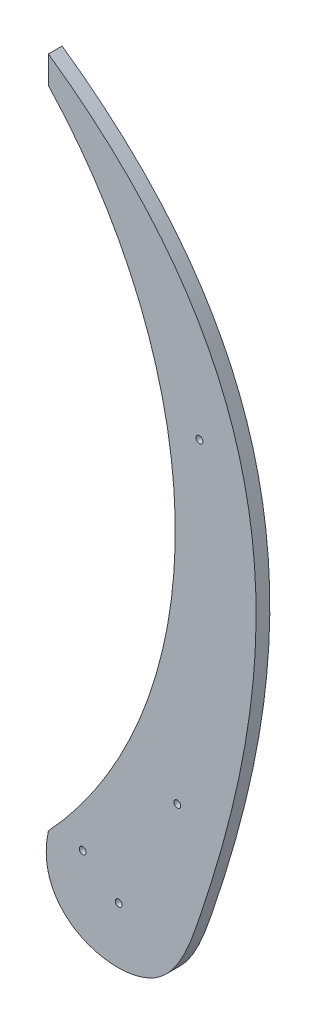
SolidWorks part; units mm, degrees
material "Mahogany"
ref_plane "Front Plane" through (0, 0, 0) normal (0, 0, 1) x (1, 0, 0)
ref_plane "Top Plane" through (0, 0, 0) normal (0, 1, 0) x (1, 0, 0)
ref_plane "Right Plane" through (0, 0, 0) normal (1, 0, 0) x (0, 0, -1)
sketch "Sketch2" plane through (0, 0, 0) normal (0, 0, 1) x (1, 0, 0)
  line L0 (0, 0) -> (110, 0) construction
  line L1 (55, 0) -> (55, -60) construction
  line L2 (0, 490) -> (0, 470)
  arc A0 (0, 0) -> (0, 470) centre (-252.5866, 235) ccw
  circle A1 centre (25, 0) radius 2.5
  circle A2 centre (51.2348, -20) radius 2.5
  circle A3 centre (93.8972, 63.809) radius 2.5
  circle A4 centre (110, 301.716) radius 2.5
  spline S0 degree 3 poles (0, 0) (-11.9512, -54.5463) (80.5487, -82.1598) (170.9865, 164.604) (184.1287, 361.0751) (0, 490) knots 0 0 0 0 0.154451 0.243977 1 1 1 1
  point P5 (0, 490)
  point P7 (0, 450)
  point P21 (0, 490)
  dimension "D3" = 450
  dimension "D4" = 345
  dimension "D6" = 5
  dimension "D10" = 5
  dimension "D1" = 110
  dimension "D2" = 490
  dimension "0" = 60
  dimension "D5" = 470
  dimension "D7" = 25
  dimension "D8" = 55
extrude "Boss-Extrude1" add sketch "Sketch2" along normal blind 10
